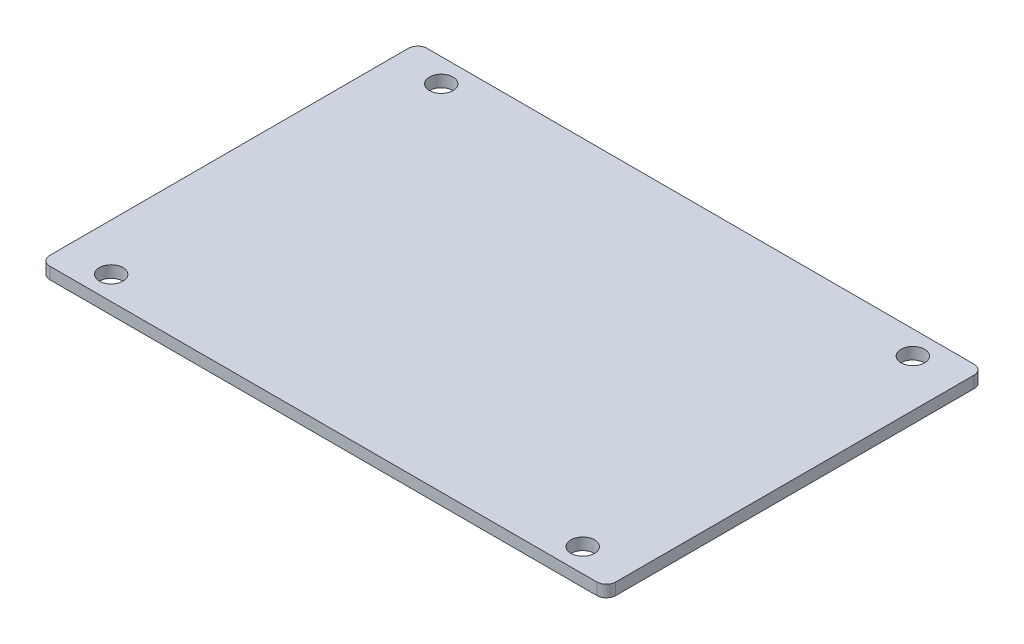
SolidWorks part; units mm, degrees
ref_plane "Front Plane" through (0, 0, 0) normal (0, 0, 1) x (1, 0, 0)
ref_plane "Top Plane" through (0, 0, 0) normal (0, 1, 0) x (1, 0, 0)
ref_plane "Right Plane" through (0, 0, 0) normal (1, 0, 0) x (0, 0, -1)
sketch "Sketch1" plane through (0, 0, 0) normal (0, 1, 0) x (1, 0, 0)
  line L1 (-64.8653, 53.014) -> (82.4547, 53.014)
  line L2 (-67.4053, 50.474) -> (-67.4053, -46.046)
  line L3 (-64.8653, -48.586) -> (82.4547, -48.586)
  line L4 (84.9947, 50.474) -> (84.9947, -46.046)
  arc A0 (-67.4053, -46.046) -> (-64.8653, -48.586) centre (-64.8653, -46.046) ccw
  arc A1 (82.4547, -48.586) -> (84.9947, -46.046) centre (82.4547, -46.046) ccw
  arc A2 (82.4547, 53.014) -> (84.9947, 50.474) centre (82.4547, 50.474) cw
  arc A3 (-64.8653, 53.014) -> (-67.4053, 50.474) centre (-64.8653, 50.474) ccw
  point P4 (-54.7053, 46.664)
  point P5 (72.2947, 46.664)
  point P6 (-54.7053, 46.664)
  point P7 (72.2947, 46.664)
  point P8 (-54.7053, -42.236)
  point P9 (72.2947, -42.236)
  point P13 (-67.4053, -48.586)
  point P18 (84.9947, 53.014)
  point P21 (-67.4053, 53.014)
  dimension "D8" = 2.54
  dimension "D1" = 101.6
  dimension "D2" = 152.4
  dimension "D3" = 127
  dimension "D4" = 88.9
  dimension "D5" = 6.35
  dimension "D6" = 12.7
  dimension "D7" = 127
  dimension "D9" = 12.7
extrude "Boss-Extrude1" add sketch "Sketch1" along normal blind 3.175
hole_wizard "Hole for #10 300® SC Nuts (SP)1" positions "Sketch3" profile "Sketch4" hole size "#10-32" standard "PEM® Inch" end condition through all
sketch "Sketch3" plane through (0, 0, 0) normal (0, -1, 0) x (-1, 0, 0)
  point P0 (-72.2947, 46.664)
  point P3 (-72.2947, -42.236)
  point P6 (54.7053, -42.236)
  point P9 (54.7053, 46.664)
sketch "Sketch4" plane through (72.2947, 0, -46.664) normal (1, 0, 0) x (0, 0, -1)
  line L0 (0, 0) -> (0, 3.175)
  line L1 (0, 3.175) -> (3.175, 3.175)
  line L2 (3.175, 3.175) -> (3.175, 0)
  line L5 (3.175, 0) -> (0, 0)
  line L11 (0, -6.35) -> (0, 107.95) construction
  dimension "Thru Hole Dia." = 6.35
  dimension "Thru Hole Depth" = 3.175
